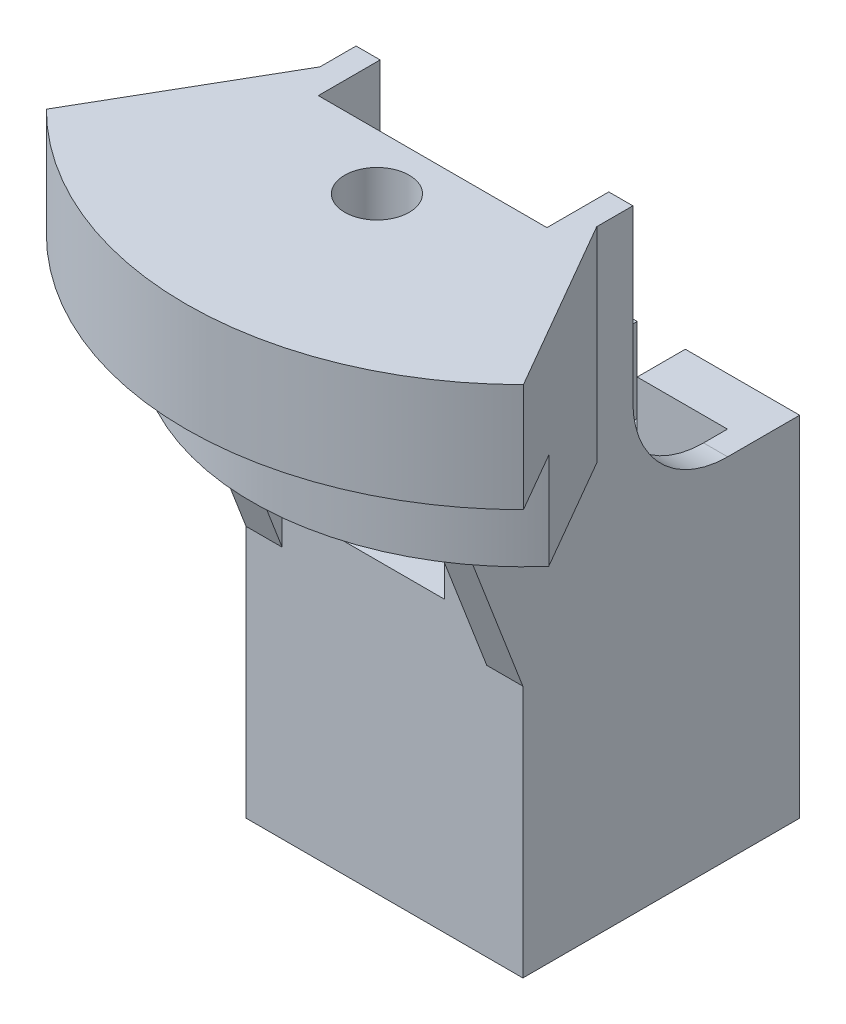
SolidWorks part; units mm, degrees
ref_plane "Front Plane" through (0, 0, 0) normal (0, 0, 1) x (1, 0, 0)
ref_plane "Top Plane" through (0, 0, 0) normal (0, 1, 0) x (1, 0, 0)
ref_plane "Right Plane" through (0, 0, 0) normal (1, 0, 0) x (0, 0, -1)
sketch "Sketch1" plane through (0, 0, 0) normal (0, 1, 0) x (1, 0, 0)
  line L1 (-14.605, -14.605) -> (14.605, -14.605)
  line L2 (-14.605, -14.605) -> (-14.605, 14.605)
  line L3 (-14.605, 14.605) -> (14.605, 14.605)
  line L4 (14.605, -14.605) -> (14.605, 14.605)
  line L5 (-14.605, -14.605) -> (14.605, 14.605) construction
  line L6 (-14.605, 14.605) -> (14.605, -14.605) construction
  point P0 (0, 0)
  dimension "D1" = 29.21
extrude "Boss-Extrude1" add sketch "Sketch1" along normal blind 41.91
sketch "Sketch2" plane through (0, 0, 0) normal (0, -1, 0) x (1, 0, 0)
  line L1 (-7.366, -7.366) -> (7.366, -7.366)
  line L2 (-7.366, -7.366) -> (-7.366, 7.366)
  line L3 (-7.366, 7.366) -> (7.366, 7.366)
  line L4 (7.366, -7.366) -> (7.366, 7.366)
  line L5 (-7.366, -7.366) -> (7.366, 7.366) construction
  line L6 (-7.366, 7.366) -> (7.366, -7.366) construction
  point P0 (0, 0)
  dimension "D1" = 14.732
extrude "Cut-Extrude1" cut sketch "Sketch2" against normal blind 8.255
sketch "Sketch3" plane through (0, 8.255, 0) normal (0, -1, 0) x (1, 0, 0)
  line L1 (-12.065, -9.525) -> (12.065, -9.525)
  line L2 (-12.065, -9.525) -> (-12.065, 9.525)
  line L3 (-12.065, 9.525) -> (12.065, 9.525)
  line L4 (12.065, -9.525) -> (12.065, 9.525)
  line L5 (-12.065, -9.525) -> (12.065, 9.525) construction
  line L6 (-12.065, 9.525) -> (12.065, -9.525) construction
  point P0 (0, 0)
  dimension "D1" = 24.13
  dimension "D2" = 19.05
extrude "Cut-Extrude2" cut sketch "Sketch3" against normal up to surface (33.655 mm away) up to face at (0, 41.91, 0)
sketch "Sketch6" plane through (0, 8.255, 0) normal (0, 1, 0) x (1, 0, 0)
  line L0 (-7.366, -7.366) -> (-7.366, 7.366) construction
  line L1 (-12.065, -2.2225) -> (-7.366, -2.2225)
  line L2 (-12.065, -2.2225) -> (-12.065, 2.2225)
  line L3 (-12.065, 2.2225) -> (-7.366, 2.2225)
  line L4 (-7.366, -2.2225) -> (-7.366, 2.2225)
  line L5 (-12.065, -2.2225) -> (-7.366, 2.2225) construction
  line L6 (-12.065, 2.2225) -> (-7.366, -2.2225) construction
  line L7 (-12.065, -9.525) -> (-12.065, 9.525) construction
  point P0 (-9.7155, 0)
  dimension "D1" = 4.445
extrude "Cut-Extrude3" cut sketch "Sketch6" against normal blind 4.445
mirror "Mirror1" about plane through (0, 0, 0) normal (1, 0, 0) of "Cut-Extrude3"
sketch "Sketch7" plane through (0, 41.91, 0) normal (0, 1, 0) x (1, 0, 0)
  line L0 (0, 0) -> (0, -2.9979) construction
  line L1 (35.4334, -2.9979) -> (-35.4334, -2.9979) construction
  line L2 (-35.4334, -2.9979) -> (-12.065, -2.9979)
  line L4 (-12.065, 9.525) -> (-12.065, -9.525) construction
  line L5 (12.065, -9.525) -> (12.065, 9.525) construction
  line L6 (12.065, -2.9979) -> (12.065, -9.525)
  line L8 (12.065, -2.9979) -> (35.4334, -2.9979)
  line L9 (12.065, -9.525) -> (-12.065, -9.525)
  line L10 (-12.065, -9.525) -> (-12.065, -2.9979)
  circle A0 centre (0, 0) radius 35.56
  point P7 (0, -2.9979)
  line M7 (12.065, 9.525) -> (12.065, -9.525)
  line M8 (12.065, -9.525) -> (-12.065, -9.525)
  line M9 (-12.065, -9.525) -> (-12.065, 9.525)
  line M10 (14.605, -14.605) -> (14.605, 14.605)
  line M12 (-14.605, 14.605) -> (-14.605, -14.605)
  line M13 (-14.605, -14.605) -> (14.605, -14.605)
  dimension "D1" = 71.12
  dimension "D2" = 2.9979
extrude "Boss-Extrude2" add sketch "Sketch7" along normal blind 27.94 contours L2 A0 L8 M10 M13 M12 | L8 L2 M7 M8 M9 M12 M13 M10
fillet "Fillet1" radius 10 2 edges at (13.335, 41.91, 2.9979) (-13.335, 41.91, 2.9979)
chamfer "Chamfer2" distance 5.08 angle 45 4 edges at (14.605, 0, 0) (0, 0, 14.605) (-14.605, 0, 0) (0, 0, -14.605)
sketch "Sketch8" plane through (0, 69.85, 0) normal (0, 1, 0) x (1, 0, 0)
  line L1 (-14.605, -2.9979) -> (-35.4334, -2.9979)
  line L2 (-14.605, -2.9979) -> (-14.605, -6.8079)
  line L3 (-14.605, -6.8079) -> (-25.1745, -25.1149)
  line L4 (-14.605, 7.0021) -> (-14.605, -2.9979) construction
  arc A2 (-35.4334, -2.9979) -> (35.4334, -2.9979) centre (0, 0) ccw construction
  arc A3 (-35.4334, -2.9979) -> (-25.1745, -25.1149) centre (0, 0) ccw
  dimension "D1" = 60
  dimension "D2" = 3.81
extrude "Cut-Extrude4" cut sketch "Sketch8" against normal up to next (27.94 mm away)
mirror "Mirror2" about plane through (0, 0, 0) normal (1, 0, 0) of "Cut-Extrude4"
sketch "Sketch9" plane through (0, 41.91, 0) normal (0, -1, 0) x (1, 0, 0)
  line L0 (-14.605, -14.605) -> (-14.605, 14.605) construction
  line L1 (-14.605, 6.8079) -> (-25.1745, 25.1149) construction
  line L2 (-14.605, 14.605) -> (14.605, 14.605) construction
  line L3 (14.605, 14.605) -> (14.605, 6.8079) construction
  line L4 (14.605, 6.8079) -> (25.1745, 25.1149) construction
  line L5 (-14.605, 6.8079) -> (-14.605, 14.605)
  line L6 (-14.605, 6.8079) -> (-25.1745, 25.1149)
  line L7 (-14.605, 14.605) -> (14.605, 14.605)
  line L8 (14.605, 14.605) -> (14.605, 6.8079)
  line L9 (14.605, 6.8079) -> (25.1745, 25.1149)
  arc A0 (25.1745, 25.1149) -> (-25.1745, 25.1149) centre (0, 0) ccw construction
  arc A1 (25.1745, 25.1149) -> (-25.1745, 25.1149) centre (0, 0) ccw
extrude "Cut-Extrude5" cut sketch "Sketch9" against normal offset from surface (16.51 mm away) 11.43 up to face at (0, 69.85, 10.5332)
sketch "Sketch10" plane through (0, 69.85, 0) normal (0, 1, 0) x (1, 0, 0)
  circle A0 centre (0, -15.5169) radius 3.3
  dimension "D1" = 15.5169
  dimension "D2" = 6.6
sketch "Sketch11" plane through (0, 58.42, 0) normal (0, -1, 0) x (-1, 0, 0)
  line L0 (14.605, -6.8079) -> (14.605, -14.605)
  line L1 (14.605, -14.605) -> (-14.605, -14.605)
  line L2 (-14.605, -14.605) -> (-14.605, -6.8079)
  line L3 (14.605, -6.8079) -> (21.525, -18.7937)
  line L5 (25.1745, -25.1149) -> (14.605, -6.8079) construction
  line L7 (-14.605, -6.8079) -> (-21.525, -18.7937)
  line L8 (-14.605, -6.8079) -> (-25.1745, -25.1149) construction
  arc A0 (21.525, -18.7937) -> (-21.525, -18.7937) centre (0, 0) cw
  dimension "D1" = 28.575
extrude "Boss-Extrude3" add sketch "Sketch11" along normal blind 10.16
hole_wizard "M6 Clearance Hole1" positions "Sketch15" profile "Sketch17" hole size "M6" standard "ANSI Metric"
sketch "Sketch15" plane through (0, 69.85, 0) normal (0, 1, 0) x (1, 0, 0)
  point P0 (0, -15.3996)
  dimension "D1" = 15.3996
sketch "Sketch17" plane through (0, 69.85, 15.3996) normal (1, 0, 0) x (0, 0, 1)
  line L0 (0, 0) -> (0, 34.5439)
  line L1 (0, 34.5439) -> (3.4016, 32.5)
  line L2 (3.4016, 32.5) -> (3.4016, 0)
  line L5 (3.4016, 0) -> (0, 0)
  line L10 (0, 34.5439) -> (-3.4016, 32.5) construction
  line L11 (0, -6.35) -> (0, 107.95) construction
  dimension "Hole Dia." = 6.8032
  dimension "Hole Depth" = 32.5
  dimension "Drill Angle" = 118
sketch "Sketch18" plane through (0, 48.26, 0) normal (0, -1, 0) x (1, 0, 0)
  line L1 (6.35, 7.366) -> (-6.35, 7.366)
  line L2 (6.35, 7.366) -> (6.35, 23.4332)
  line L3 (6.35, 23.4332) -> (-6.35, 23.4332)
  line L4 (-6.35, 7.366) -> (-6.35, 23.4332)
  line L5 (6.35, 7.366) -> (-6.35, 23.4332) construction
  line L6 (6.35, 23.4332) -> (-6.35, 7.366) construction
  line L8 (7.366, 7.366) -> (-7.366, 7.366) construction
  point P0 (0, 15.3996)
  dimension "D1" = 12.7
extrude "Cut-Extrude9" cut sketch "Sketch18" along normal blind 12.7
extrude "Cut-Extrude6" [suppressed] cut sketch "Sketch10" against normal blind 35
sketch "Sketch13" plane through (0, 48.26, 0) normal (0, -1, 0) x (1, 0, 0)
  line L0 (-14.605, 14.605) -> (-6.35, 14.605) construction
  line L1 (-6, 14.605) -> (6, 14.605)
  line L2 (-6, 14.605) -> (-6, 9.525)
  line L3 (-6, 9.525) -> (6, 9.525)
  line L4 (6, 14.605) -> (6, 9.525)
  line L5 (12.065, 9.525) -> (-12.065, 9.525) construction
  point P8 (0, 9.525)
  dimension "D1" = 12
extrude "Cut-Extrude8" [suppressed] cut sketch "Sketch13" along normal up to surface (10.87 mm away)
sketch "Sketch14" plane through (-14.605, 0, 0) normal (-1, 0, 0) x (0, 0, 1)
  line L0 (14.605, 48.26) -> (20.955, 48.26)
  line L1 (18.7937, 48.26) -> (28.575, 48.26) construction
  line L2 (20.955, 48.26) -> (14.605, 31.75)
  line L3 (14.605, 48.26) -> (14.605, 5.08) construction
  line L4 (14.605, 31.75) -> (14.605, 48.26)
  dimension "D1" = 6.35
  dimension "D2" = 16.51
extrude "Boss-Extrude4" add sketch "Sketch14" against normal blind 3.81
mirror "Mirror3" about plane through (0, 0, 0) normal (1, 0, 0) of "Boss-Extrude4"
sketch "Sketch19" plane through (0, 41.91, 0) normal (0, 1, 0) x (1, 0, 0)
  line L0 (12.065, 9.525) -> (-12.065, 9.525) construction
  line L1 (2.54, 14.605) -> (-2.54, 14.605)
  line L2 (2.54, 14.605) -> (2.54, 9.525)
  line L3 (2.54, 9.525) -> (-2.54, 9.525)
  line L4 (-2.54, 14.605) -> (-2.54, 9.525)
  line L5 (2.54, 14.605) -> (-2.54, 9.525) construction
  line L6 (2.54, 9.525) -> (-2.54, 14.605) construction
  line L7 (14.605, 14.605) -> (-14.605, 14.605) construction
  point P0 (0, 12.065)
  dimension "D1" = 5.08
extrude "Cut-Extrude10" cut sketch "Sketch19" against normal blind 8.89
